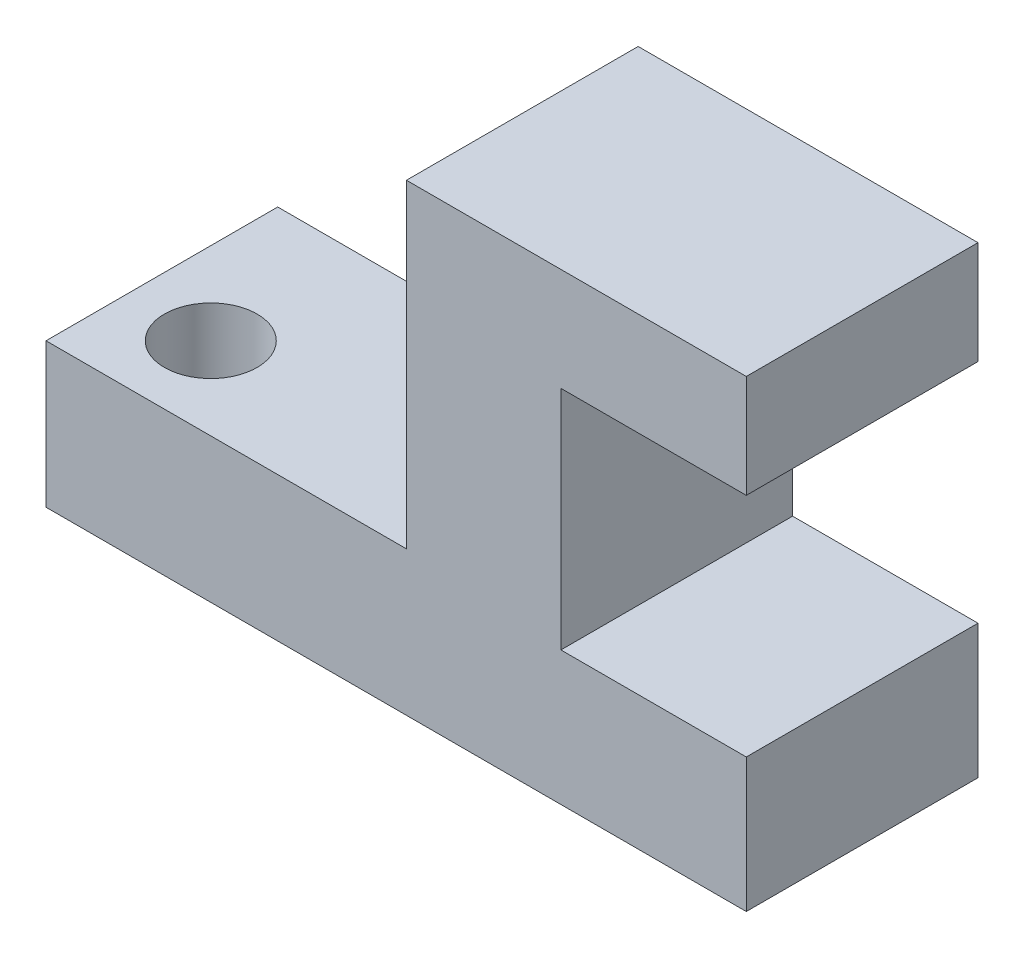
SolidWorks part; units mm, degrees
material "6061 Alloy"
ref_plane "Front Plane" through (0, 0, 0) normal (0, 0, 1) x (1, 0, 0)
ref_plane "Top Plane" through (0, 0, 0) normal (0, 1, 0) x (1, 0, 0)
ref_plane "Right Plane" through (0, 0, 0) normal (1, 0, 0) x (0, 0, -1)
sketch "Sketch1" plane through (0, 0, 0) normal (0, 0, 1) x (1, 0, 0)
  line L0 (0, 0) -> (-13.6, 0)
  line L1 (-13.6, 0) -> (-13.6, 2.8)
  line L2 (-13.6, 2.8) -> (-6.6, 2.8)
  line L3 (-6.6, 2.8) -> (-6.6, 9)
  line L4 (-6.6, 9) -> (0, 9)
  line L5 (0, 9) -> (0, 7)
  line L6 (0, 7) -> (-3.6, 7)
  line L7 (-3.6, 7) -> (-3.6, 2.6)
  line L8 (-3.6, 2.6) -> (0, 2.6)
  line L9 (0, 2.6) -> (0, 0)
  dimension "D1" = 2
  dimension "D2" = 2.6
  dimension "D3" = 3
  dimension "D4" = 3.6
  dimension "D5" = 4.4
  dimension "D6" = 7
  dimension "D7" = 2.8
extrude "Boss-Extrude1" add sketch "Sketch1" along normal blind 4.5
sketch "Sketch2" plane through (0, 2.8, 0) normal (0, 1, 0) x (1, 0, 0)
  line L0 (-6.6, -4.5) -> (-13.6, -4.5) construction
  line L1 (-6.6, 0) -> (-13.6, 0) construction
  line L2 (-13.6, -4.5) -> (-13.6, 0) construction
  line L3 (-6.6, -4.5) -> (-6.6, 0) construction
  circle A0 centre (-8.2, -1.6) radius 0.9
  circle A1 centre (-12, -2.9) radius 0.9
  dimension "D1" = 1.8
  dimension "D2" = 1.8
  dimension "D3" = 1.6
  dimension "D4" = 1.6
  dimension "D5" = 1.6
  dimension "D6" = 1.6
extrude "Cut-Extrude1" cut sketch "Sketch2" against normal blind 10
